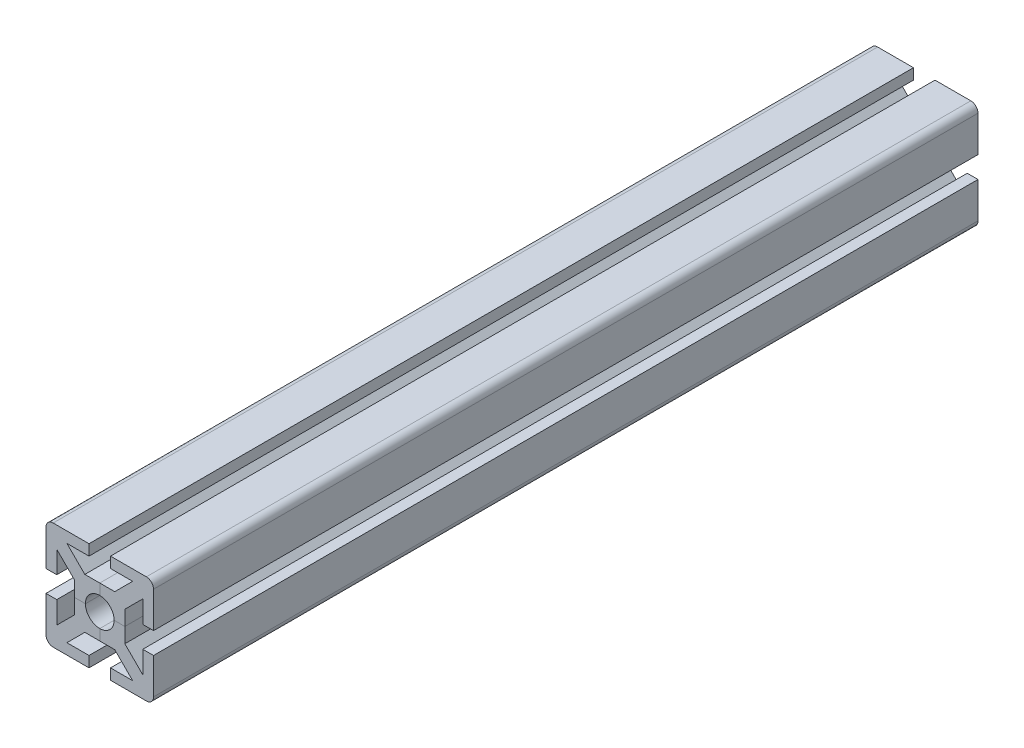
SolidWorks part; units mm, degrees
ref_plane "Alzado" through (0, 0, 0) normal (0, 0, 1) x (1, 0, 0)
ref_plane "Planta" through (0, 0, 0) normal (0, 1, 0) x (1, 0, 0)
ref_plane "Vista lateral" through (0, 0, 0) normal (1, 0, 0) x (0, 0, -1)
sketch "Croquis1" plane through (0, 0, 0) normal (0, 0, 1) x (1, 0, 0)
  line L0 (0, 0) -> (50000, 0) construction
  line L1 (-15, 15) -> (15, 15) construction
  line L2 (-15, 15) -> (-15, -15) construction
  line L3 (-15, -15) -> (15, -15) construction
  line L4 (15, 15) -> (15, -15) construction
  line L5 (-15, 15) -> (15, -15) construction
  line L6 (-15, -15) -> (15, 15) construction
  line L7 (0, 0) -> (0, -50000) construction
  line L8 (0, 4) -> (0, 7)
  line L9 (0, 7) -> (4.1716, 7)
  line L10 (4.1716, 7) -> (9.1716, 12)
  line L11 (9.1716, 12) -> (3, 12)
  line L12 (3, 12) -> (3, 15)
  line L13 (3, 15) -> (15, 15)
  line L20 (2.8284, 2.8284) -> (15, 15)
  arc A0 (2.8284, 2.8284) -> (0, 4) centre (0, 0) ccw
  point P0 (0, 0)
  dimension "D3" = 4
  dimension "D1" = 30
  dimension "D2" = 6
  dimension "D4" = 8
  dimension "D5" = 3
  dimension "D6" = 2
extrude "Saliente-Extruir1" add sketch "Croquis1" along normal mid plane 230
mirror "Simetría1" about plane through (2.8284, 2.8284, 115) normal (-0.7071, 0.7071, 0) of "Saliente-Extruir1"
fillet "Redondeo1" radius 2 1 edges at (15, 15, 0)
pattern_circular "MatrizC4" count 4 over 360 about axis through (0, 0, 0) along (0, 0, 1) of bodies 102
